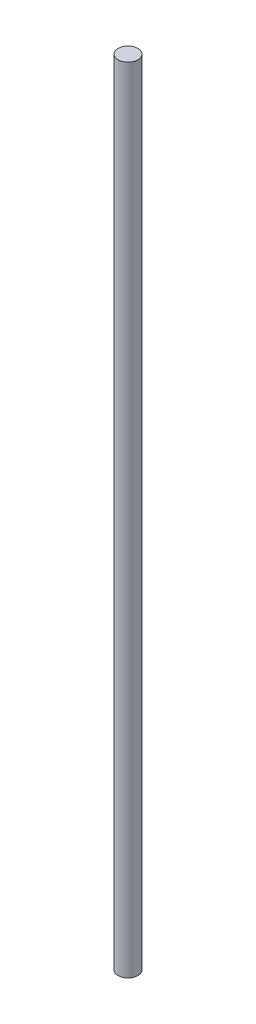
SolidWorks part; units mm, degrees
ref_plane "Front" through (0, 0, 0) normal (0, 0, 1) x (1, 0, 0)
ref_plane "Top" through (0, 0, 0) normal (0, 1, 0) x (1, 0, 0)
ref_plane "Right" through (0, 0, 0) normal (1, 0, 0) x (0, 0, -1)
sketch "Sketch1" plane through (0, 0, 0) normal (0, 1, 0) x (1, 0, 0)
  circle A0 centre (0, 0) radius 3.175
  dimension "D1" = 6.35
extrude "Boss-Extrude1" add sketch "Sketch1" along normal blind 254
